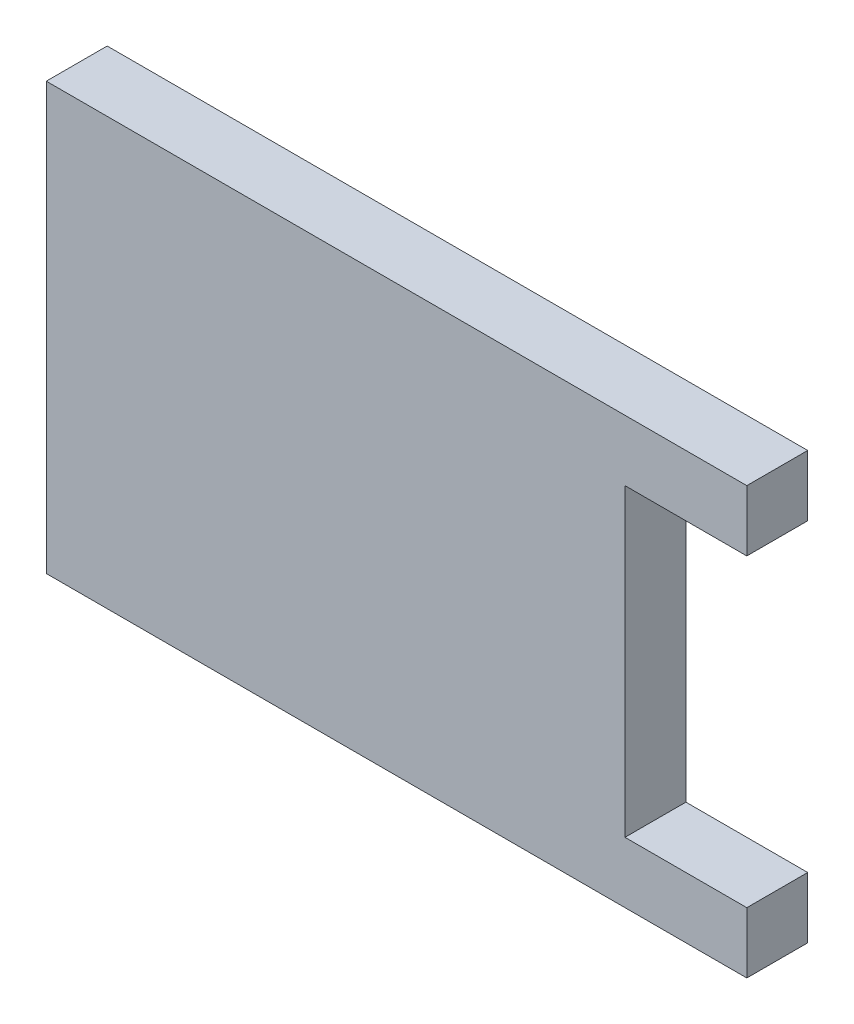
SolidWorks part; units mm, degrees
ref_plane "Front Plane" through (0, 0, 0) normal (0, 0, 1) x (1, 0, 0)
ref_plane "Top Plane" through (0, 0, 0) normal (0, 1, 0) x (1, 0, 0)
ref_plane "Right Plane" through (0, 0, 0) normal (1, 0, 0) x (0, 0, -1)
sketch "Sketch1" plane through (0, 0, 0) normal (0, 0, 1) x (1, 0, 0)
  line L1 (-11.5, 7) -> (11.5, 7)
  line L2 (-11.5, 7) -> (-11.5, -7)
  line L3 (-11.5, -7) -> (11.5, -7)
  line L4 (11.5, 7) -> (11.5, -7)
  point P4 (11.5, 0)
  point P6 (0, 7)
  dimension "D1" = 14
  dimension "D2" = 23
extrude "Extrude1" add sketch "Sketch1" along normal blind 2
sketch "Sketch3" plane through (0, 0, 2) normal (0, 0, 1) x (1, 0, 0)
  line L0 (11.5, 0) -> (-11.5, 0) construction
  line L1 (11.5, 5) -> (7.5, 5)
  line L2 (11.5, 5) -> (11.5, -5)
  line L3 (11.5, -5) -> (7.5, -5)
  line L4 (7.5, 5) -> (7.5, -5)
  line L5 (11.5, -7) -> (11.5, 7) construction
  line L6 (-11.5, 7) -> (-11.5, -7) construction
  point P11 (11.5, 0)
  dimension "D1" = 4
  dimension "D2" = 10
extrude "Extrude3" cut sketch "Sketch3" against normal blind 2
